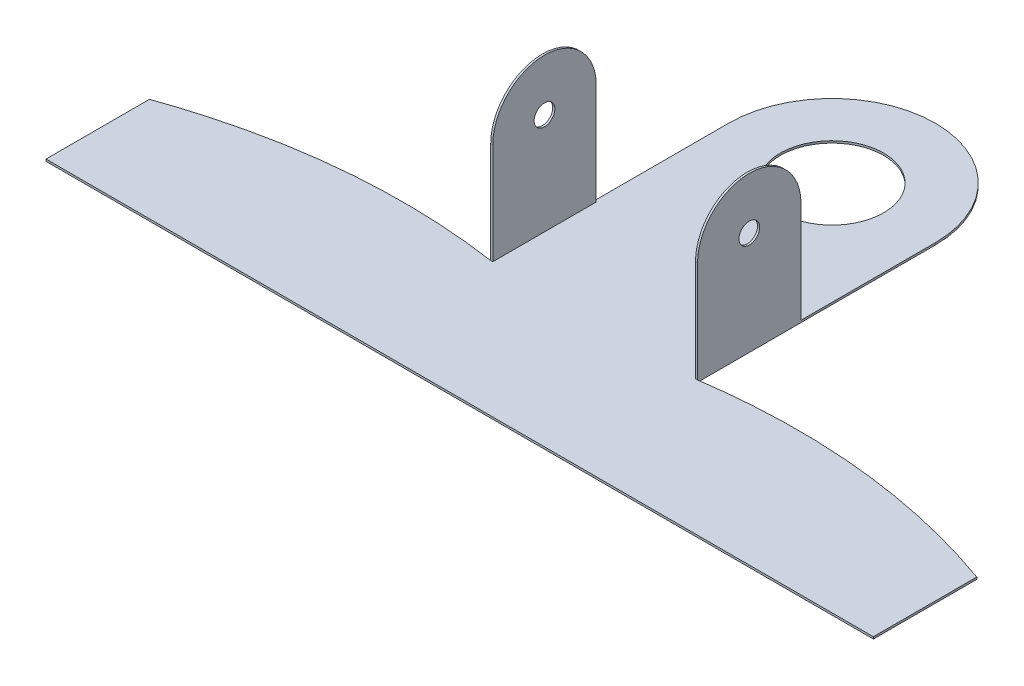
SolidWorks part; units mm, degrees
ref_plane "前视基准面" through (0, 0, 0) normal (0, 0, 1) x (1, 0, 0)
ref_plane "上视基准面" through (0, 0, 0) normal (0, 1, 0) x (1, 0, 0)
ref_plane "右视基准面" through (0, 0, 0) normal (1, 0, 0) x (0, 0, -1)
sketch "草图1" plane through (0, 0, 0) normal (0, 1, 0) x (1, 0, 0)
  line L0 (10, 0) -> (10, -23)
  line L1 (40, -26) -> (40, -36)
  line L2 (40, -36) -> (-40, -36)
  line L3 (0, 21.1303) -> (0, -58.7304) construction
  line L4 (-10, 0) -> (-10, -23)
  line L5 (-40, -26) -> (-40, -36)
  circle A0 centre (0, 0) radius 5
  arc A1 (10, 0) -> (-10, 0) centre (0, 0) ccw
  spline S0 degree 2 poles (10, -23) (25.2853, -20.7809) (40, -26) knots 0 0 0 1 1 1
  spline S1 degree 2 poles (-10, -23) (-25.2853, -20.7809) (-40, -26) knots 0 0 0 1 1 1
  point P15 (0, -36)
  dimension "D1" = 30
  dimension "D2" = 3
  dimension "D3" = 10
extrude "凸台-拉伸1" add sketch "草图1" along normal mid plane 0.2
sketch "草图3" plane through (10, 0, 0) normal (1, 0, 0) x (0, 0, -1)
  line L1 (-23, -0.1) -> (-13, -0.1)
  line L2 (-23, -0.1) -> (-23, 9.9)
  line L4 (-13, -0.1) -> (-13, 9.9)
  arc A0 (-13, 9.9) -> (-23, 9.9) centre (-18, 9.9) ccw
  circle A1 centre (-18, 9.9) radius 1
  dimension "D1" = 10
  dimension "D2" = 10
extrude "凸台-拉伸2" add sketch "草图3" against normal blind 0.2
sketch "草图4" plane through (-10, 0, 0) normal (-1, 0, 0) x (0, 0, 1)
  line L1 (23, -0.1) -> (13, -0.1)
  line L2 (23, -0.1) -> (23, 9.9)
  line L4 (13, -0.1) -> (13, 9.9)
  arc A0 (23, 9.9) -> (13, 9.9) centre (18, 9.9) ccw
  circle A1 centre (18, 9.9) radius 1
  dimension "D1" = 10
  dimension "D2" = 10
extrude "凸台-拉伸3" add sketch "草图4" against normal blind 0.2
